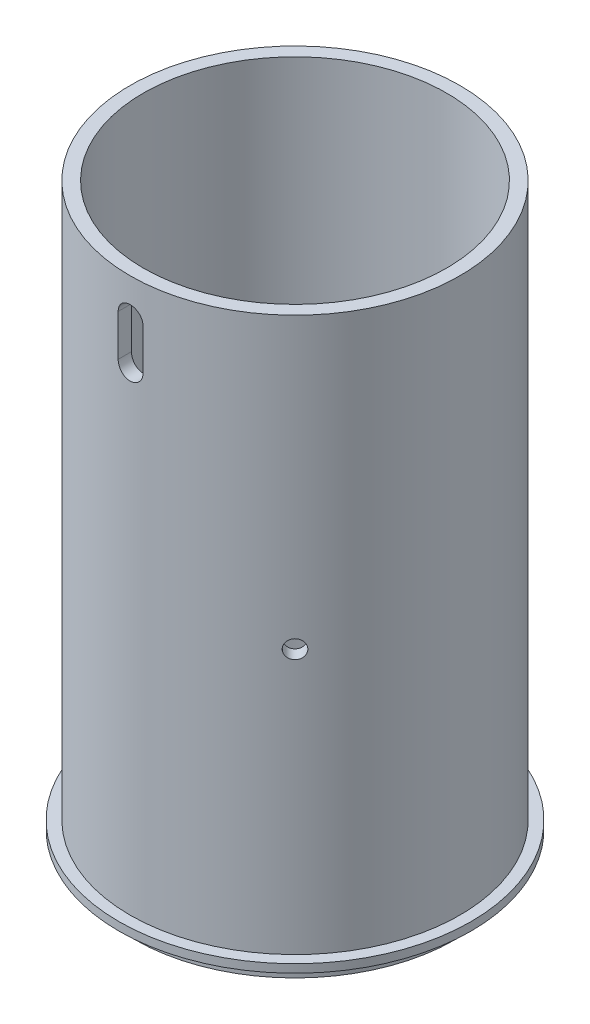
SolidWorks part; units mm, degrees
material "6061-T6 (SS)"
ref_plane "Front Plane" through (0, 0, 0) normal (0, 0, 1) x (1, 0, 0)
ref_plane "Top Plane" through (0, 0, 0) normal (0, 1, 0) x (1, 0, 0)
ref_plane "Right Plane" through (0, 0, 0) normal (1, 0, 0) x (0, 0, -1)
sketch "Sketch1" plane through (0, 0, 0) normal (0, 1, 0) x (1, 0, 0)
  circle A0 centre (0, 0) radius 18.2245
  circle A1 centre (0, 0) radius 24.5999
  dimension "D1" = 49.1998
  dimension "D2" = 36.449
extrude "Boss-Extrude1" add sketch "Sketch1" along normal blind 4.3942
sketch "Sketch2" plane through (0, 4.3942, 0) normal (0, 1, 0) x (1, 0, 0)
  circle A1 centre (0, 0) radius 25.3365
  circle A2 centre (0, 0) radius 18.2245 construction
  circle A3 centre (0, 0) radius 18.2245
  dimension "D1" = 50.673
extrude "Boss-Extrude2" add sketch "Sketch2" along normal blind 33.02
thread "Thread1" [suppressed] pitch 1.4111 start angle 0, offset 0, length 0, pitch 1.4111, diameter 38.1
ref_plane "Plane1" through (-19.05, 17.0942, 0) normal (0, 0, 1) x (-1, 0, 0)
sketch "Thread Profile1" plane through (-19.05, 17.0942, 0) normal (0, 0, 1) x (-1, 0, 0)
  line L0 (0, 0) -> (0, 1.4111) construction
  line L11 (0, 0) -> (0, 1.0581)
  line L12 (0, 1.0581) -> (-0.7645, 0.6167)
  line L13 (-0.7645, 0.6167) -> (-0.7645, 0.4414)
  line L15 (-0.7645, 0.4414) -> (0, 0)
  line L17 (-0.7645, 0.529) -> (0, 0.529) construction
  point P2 (0, 0)
  dimension "Pitch" = 1.4111
  dimension "Profile_Angle" = 60
  dimension "Profile_Land" = 0.1753
  dimension "Profile_Height" = 0.7645
sketch "Sketch15" plane through (0, 4.3942, 0) normal (0, -1, 0) x (1, 0, 0)
  circle A0 centre (0, 0) radius 25.3365 construction
  circle A2 centre (0, 0) radius 27.051
  circle A3 centre (0, 0) radius 25.3365
  dimension "D1" = 54.102
extrude "Boss-Extrude3" add sketch "Sketch15" against normal blind 1.27
sketch "Sketch16" plane through (0, 0, 0) normal (0, -1, 0) x (1, 0, 0)
  circle A0 centre (0, 0) radius 24.5999 construction
  circle A1 centre (0, 0) radius 24.5999
extrude "Cut-Extrude1" [suppressed] cut sketch "Sketch16" along normal blind 2.54
sketch "Sketch17" plane through (0, 0, 0) normal (0, -1, 0) x (1, 0, 0)
  circle A2 centre (0, 0) radius 19.685
  circle A3 centre (0, 0) radius 24.5999 construction
  circle A4 centre (0, 0) radius 24.5999
  dimension "D1" = 39.37
sketch "Sketch18" plane through (0, 37.4142, 0) normal (0, 1, 0) x (1, 0, 0)
  circle A10 centre (0, 0) radius 25.3365 construction
  circle A11 centre (0, 0) radius 25.3365
  circle A12 centre (0, 0) radius 23.3045
  dimension "D1" = 2.032
extrude "Boss-Extrude5" add sketch "Sketch18" along normal blind 53.34
ref_plane "Plane2" through (0, 0, 25.3365) normal (0, 0, 1) x (1, 0, 0)
sketch "Sketch19" plane through (0, 0, 25.3365) normal (0, 0, 1) x (1, 0, 0)
  line L0 (0, 85.0252) -> (0, 78.6498) construction
  line L1 (1.905, 85.0252) -> (1.905, 78.6498)
  line L2 (-1.905, 85.0252) -> (-1.905, 78.6498)
  arc A0 (1.905, 85.0252) -> (-1.905, 85.0252) centre (0, 85.0252) ccw
  arc A1 (-1.905, 78.6498) -> (1.905, 78.6498) centre (0, 78.6498) ccw
  point P4 (0, 81.8375)
  dimension "D1" = 3.81
extrude "Cut-Extrude2" cut sketch "Sketch19" against normal blind 10.16
ref_plane "Plane3" through (-17.9156, 0, 17.9156) normal (-0.7071, 0, 0.7071) x (0, -1, 0)
sketch "Sketch20" plane through (-17.9156, 0, 17.9156) normal (-0.7071, 0, 0.7071) x (0, -1, 0)
  line L0 (-90.7542, 25.3365) -> (-90.7542, -25.3365) construction
  point P0 (-46.3042, 0)
  dimension "D1" = 44.45
hole_wizard "#35 (0.11) Diameter Hole1" positions "Sketch20" profile "Sketch21" hole size "#35" standard "ANSI Inch"
sketch "Sketch21" plane through (-17.9156, 46.3042, 17.9156) normal (0, 1, 0) x (0.7071, 0, 0.7071)
  line L0 (0, 0) -> (0, 2.032)
  line L1 (0, 2.032) -> (1.397, 2.032)
  line L2 (1.397, 2.032) -> (1.397, 0)
  line L5 (1.397, 0) -> (0, 0)
  line L11 (0, -6.35) -> (0, 107.95) construction
  dimension "Thru Hole Dia." = 2.794
  dimension "Thru Hole Depth" = 2.032
pattern_circular "CirPattern1" count 4 over 360 about axis through (0, 37.4142, 0) along (0, -1, 0) of "#35 (0.11) Diameter Hole1"
other "Move Face1" face at (0, 0, 24.5999) parameters "D1"=2.032
other "Move Face2" face at (0, 37.4142, 18.2245) parameters "D1"=5.08
